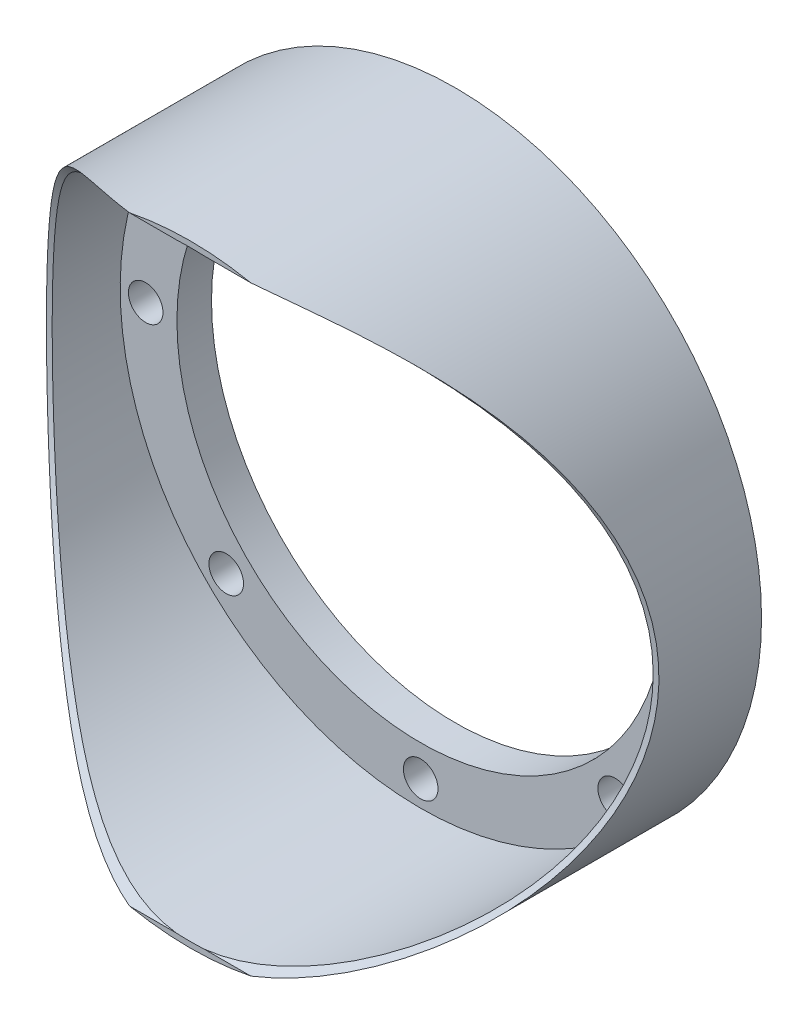
SolidWorks part; units mm, degrees
material "6063-T4"
ref_plane "Front Plane" through (0, 0, 0) normal (0, 0, 1) x (1, 0, 0)
ref_plane "Top Plane" through (0, 0, 0) normal (0, 1, 0) x (1, 0, 0)
ref_plane "Right Plane" through (0, 0, 0) normal (1, 0, 0) x (0, 0, -1)
sketch "Sketch1" plane through (0, 0, 0) normal (0, 0, 1) x (1, 0, 0)
  line L0 (0, 0) -> (490.2841, 0) construction
  line L1 (0, 0) -> (350.0755, 350.0755) construction
  line L2 (0, 0) -> (-298.905, 298.905) construction
  line L3 (0, 0) -> (-282.8341, -282.8341) construction
  line L4 (0, 0) -> (233.7979, -233.7979) construction
  line L5 (0, 0) -> (0, 312.9098) construction
  line L6 (0, 0) -> (-348.2385, 0) construction
  line L7 (0, 0) -> (0, -336.5434) construction
  line L8 (0, 0) -> (425.213, 113.9355) construction
  line L9 (0, 0) -> (-424.8399, 113.8355) construction
  line L10 (0, 0) -> (-167.2069, -403.6731) construction
  circle A0 centre (0, 0) radius 211.5
  circle A1 centre (0, 0) radius 265.7
  circle A2 centre (0, 0) radius 238.6 construction
  circle A3 centre (238.6, 0) radius 20
  circle A4 centre (168.7157, 168.7157) radius 20
  circle A5 centre (0, 238.6) radius 20
  circle A6 centre (-168.7157, 168.7157) radius 20
  circle A7 centre (-238.6, 0) radius 20
  circle A8 centre (-168.7157, -168.7157) radius 20
  circle A9 centre (0, -238.6) radius 20
  circle A10 centre (168.7157, -168.7157) radius 20
  circle A11 centre (230.4699, 61.7542) radius 5
  circle A12 centre (-230.4699, 61.7542) radius 5
  circle A13 centre (-91.3083, -220.4377) radius 5
  point P13 (168.7157, 168.7157)
  point P14 (238.6, 0)
  point P15 (168.7157, -168.7157)
  point P16 (0, -238.6)
  point P17 (-168.7157, -168.7157)
  point P18 (-238.6, 0)
  point P19 (-168.7157, 168.7157)
  point P20 (0, 238.6)
  point P37 (230.4699, 61.7542)
  point P41 (-230.4699, 61.7542)
  point P42 (-91.3083, -220.4377)
extrude "Extrude1" add sketch "Sketch1" along normal blind 5
sketch "Sketch2" plane through (0, 0, 5) normal (0, 0, 1) x (1, 0, 0)
  circle A0 centre (238.6, 0) radius 15
  circle A1 centre (168.7157, 168.7157) radius 15
  circle A2 centre (0, 238.6) radius 15
  circle A3 centre (-168.7157, 168.7157) radius 15
  circle A4 centre (-238.6, 0) radius 15
  circle A5 centre (-168.7157, -168.7157) radius 15
  circle A6 centre (0, -238.6) radius 15
  circle A7 centre (168.7157, -168.7157) radius 15
  circle A8 centre (0, 0) radius 265.7
  circle A9 centre (0, 0) radius 211.5
  point P0 (238.6, 0)
  point P1 (168.7157, 168.7157)
  point P3 (0, 238.6)
  point P5 (-168.7157, 168.7157)
  point P7 (-238.6, 0)
  point P9 (-168.7157, -168.7157)
  point P11 (168.7157, -168.7157)
  point P13 (0, -238.6)
extrude "Extrude2" add sketch "Sketch2" along normal blind 25
sketch "Sketch3" plane through (0, 0, 30) normal (0, 0, 1) x (1, 0, 0)
  circle A0 centre (0, 0) radius 265.7
  circle A1 centre (0, 0) radius 260.7
extrude "Extrude3" add sketch "Sketch3" along normal blind 200
sketch "Sketch4" plane through (0, 0, 0) normal (1, 0, 0) x (0, 0, -1)
  line L2 (0, 0) -> (-508.4098, 0) construction
  circle A0 centre (-400, 0) radius 311
  point P0 (-400, 0)
  dimension "D1" = 400
extrude "Extrude4" cut sketch "Sketch4" along normal through all and the other way through all
